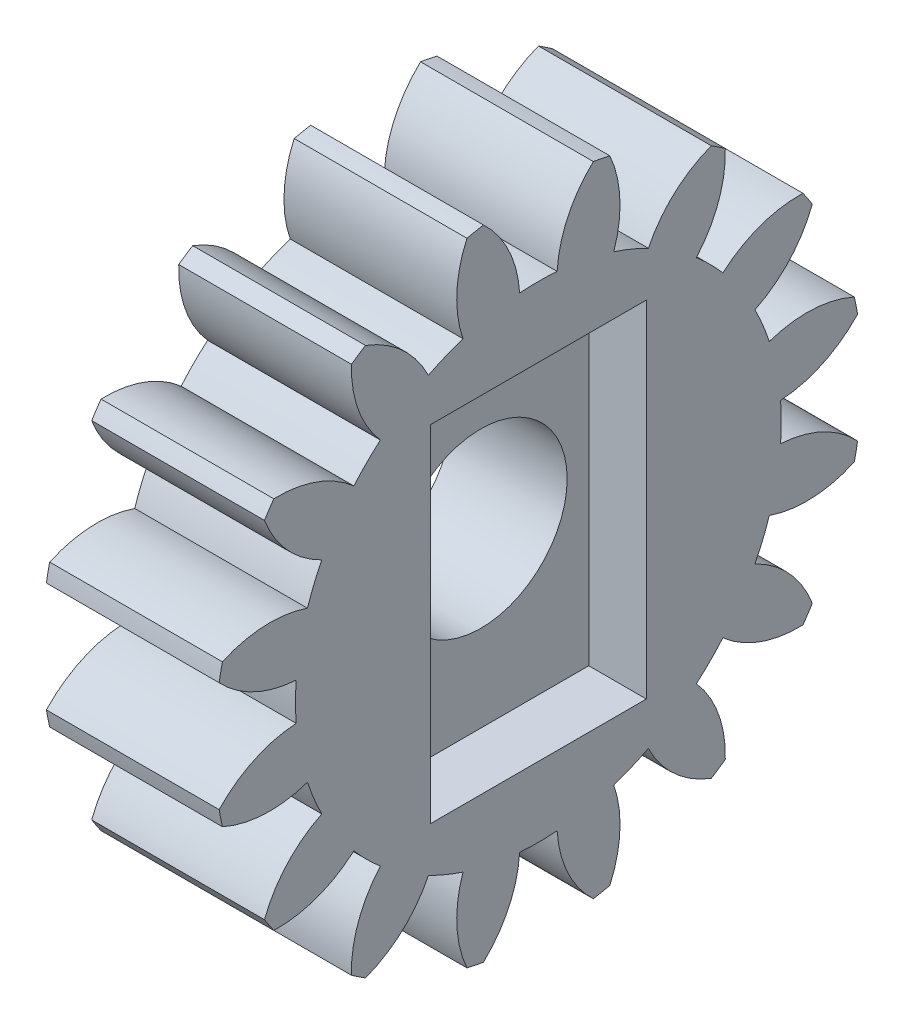
SolidWorks part; units mm, degrees
ref_plane "Plane1" through (0, 0, 0) normal (0, 0, 1) x (1, 0, 0)
ref_plane "Plane2" through (0, 0, 0) normal (0, 1, 0) x (1, 0, 0)
ref_plane "Plane3" through (0, 0, 0) normal (1, 0, 0) x (0, 0, -1)
sketch "HoldingSke" plane through (0, 0, 0) normal (0, 1, 0) x (1, 0, 0)
  line L0 (0, 0) -> (0.769, -0.2205)
  line L1 (-15, 0) -> (100, 0) construction
  line L2 (0, 0) -> (-2.1039, 2.3779)
  line L3 (0, 0) -> (-11.863, 4.5341)
  line L4 (0, 0) -> (8.3015, 2.3804)
  line L5 (0, 0) -> (-46.8476, -17.4728)
  line L6 (0, 0) -> (-4.9738, -3.3558)
  line L7 (-2.1039, 2.3779) -> (8.6586, 51.2059)
  line L8 (-76.2, 54.61) -> (-75.9, 54.61)
  line L9 (-71.009, 38.7566) -> (-53.1078, 45.2721)
  line L10 (-76.2, 71.12) -> (104.1128, 71.12)
  line L11 (0, 0) -> (-6, 0)
  line L12 (-76.2, 101.6) -> (-76.155, 101.6)
  line L13 (24.9733, 27.94) -> (52.9518, 28.4284)
  line L14 (24.9733, 27.94) -> (24.9743, 27.94)
  line L15 (24.9733, 27.94) -> (100.4006, 29.5858)
  line L16 (-63.627, -1.25) -> (-12.827, -1.25)
  circle A0 centre (0, 0) radius 1
  circle A1 centre (0, 0) radius 8.4365
  circle A2 centre (0, 0) radius 37.5
  circle A3 centre (0, 0) radius 1
  dimension "MHD" = 16.873
  dimension "Hub_dia" = 75
  dimension "Bore" = 2
  dimension "MBD" = 2
  dimension "Num_teeth" = 16
  dimension "Pitch" = 0.8
  dimension "Overall_len" = 50
  dimension "Show_teeth" = 16
  dimension "Thickness" = 6
  dimension "OAL" = 50.0001
  dimension "T_dim" = 0.3
  dimension "Ap" = 20
  dimension "H" = 19.05
  dimension "Pitch_radius" = 180.3128
  dimension "Width" = 6
  dimension "Backlash" = 0.045
  dimension "Addendum_fac" = 1
  dimension "Dedendum_fac" = 1.25
  dimension "Clearance_fac" = 0.25
  dimension "Dedendum_add" = 0.001
  dimension "Module" = 1.25
sketch "BasProSke" plane through (0, 0, 0) normal (0, 1, 0) x (1, 0, 0)
  line L0 (-10, 0) -> (60, 0) construction
  line L1 (0, 0) -> (0, 11.25)
  line L2 (0, 0) -> (6, 0)
  line L3 (6, 0) -> (6, 11.25)
  line L4 (6, 11.25) -> (0, 11.25)
  dimension "Thickness" = 6
  dimension "Diameter" = 22.5
revolve "Base-Revolve" add sketch "BasProSke" angle 360 about L0
sketch "TooCutSke" plane through (0, 0, 0) normal (1, 0, 0) x (0, 0, -1)
  line L1 (0, 0) -> (0, 107) construction
  line L2 (0, 0) -> (-1.0589, 9.9438) construction
  line L3 (0, 0) -> (-3.8859, 19.5358) construction
  line L4 (-1.0589, 9.9438) -> (-1.943, 9.7679) construction
  arc A0 (0.6511, 8.4113) -> (-0.6511, 8.4113) centre (0, 0) ccw
  arc A1 (1.9309, 11.1088) -> (-1.9309, 11.1088) centre (0, 0) ccw
  circle A2 centre (0, 0) radius 10 construction
  circle A3 centre (0, 0) radius 9.3969 construction
  arc A4 (-0.6511, 8.4113) -> (-1.9309, 11.1088) centre (-4.6437, 8.1693) ccw
  arc A5 (1.9309, 11.1088) -> (0.6511, 8.4113) centre (4.6437, 8.1693) ccw
  dimension "Root_dia" = 16.873
  dimension "Overcut_dia" = 22.5508
  dimension "Pitch_dia" = 20
  dimension "Base_dia" = 18.7939
  dimension "Flank_rad" = 4
  dimension "Half_ang" = 11.25
  dimension "Half_CT" = 0.9014
extrude "ToothCut" cut sketch "TooCutSke" along normal through all
fillet "Breaks" [suppressed] radius 0.025
fillet "RootFillets" [suppressed] radius 0.3135
pattern_circular "TeethCuts" count 16 every 22.5 about axis through (-10, 0, 0) along (1, 0, 0) of "ToothCut", "RootFillets", "Breaks"
sketch "HubNeaOneSke" plane through (0, 0, 0) normal (-1, 0, 0) x (0, 0, 1)
  circle A0 centre (0, 0) radius 8.4365
  dimension "Diameter" = 16.873
extrude "HubNearOne" [suppressed] add sketch "HubNeaOneSke" along normal blind 44.0001
sketch "HubNeaBotSke" plane through (0, 0, 0) normal (-1, 0, 0) x (0, 0, 1)
  circle A0 centre (0, 0) radius 8.4365
  dimension "Diameter" = 16.873
extrude "HubNearBoth" [suppressed] add sketch "HubNeaBotSke" along normal blind 22
ref_plane "FarPln" through (6, 0, 0) normal (1, 0, 0) x (0, 0, -1)
sketch "HubFarSke" plane through (6, 0, 0) normal (1, 0, 0) x (0, 0, -1)
  circle A0 centre (0, 0) radius 8.4365
  dimension "Diameter" = 16.873
extrude "HubFar" [suppressed] add sketch "HubFarSke" along normal blind 22
sketch "BorSke" plane through (0, 0, 0) normal (1, 0, 0) x (0, 0, -1)
  circle A0 centre (0, 0) radius 3
  dimension "D1" = 6
extrude "Bore" cut sketch "BorSke" along normal mid plane 100.0001
sketch "KeySke" plane through (0, 0, 0) normal (1, 0, 0) x (0, 0, -1)
  line L0 (-0.4, 0) -> (-0.4, 1.3)
  line L1 (-0.4, 1.3) -> (0.4, 1.3)
  line L2 (0.4, 1.3) -> (0.4, 0)
  line L3 (0, 0) -> (0, 34) construction
  line L4 (-0.4, 0) -> (0.4, 0)
  dimension "Offset" = 1.3
  dimension "Width" = 0.8
extrude "Keyway" [suppressed] cut sketch "KeySke" along normal mid plane 100.0001
pattern_circular "Keyway2" [suppressed] count 2 every 90 about axis through (-10, 0, 0) along (1, 0, 0)
sketch "Эскиз1" plane through (6, 0, 0) normal (1, 0, 0) x (0, 0, -1)
  line L0 (0, 7.148) -> (0, -6.7262) construction
  line L1 (-7.5704, 0) -> (7.5314, 0) construction
  line L3 (-3.75, 6) -> (3.75, 6)
  line L4 (-3.75, 6) -> (-3.75, -6)
  line L5 (-3.75, -6) -> (3.75, -6)
  line L6 (3.75, 6) -> (3.75, -6)
  dimension "D1" = 7.5
  dimension "D2" = 12
extrude "Вырез-Вытянуть1" cut sketch "Эскиз1" against normal blind 2
equation "' \"Module@HoldingSke\" = 6.35"
equation "' \"Num_teeth@HoldingSke\" = 12"
equation "' \"Ap@HoldingSke\" =  20"
equation "' \"Ap@HoldingSke\" = 20"
equation "' \"Width@HoldingSke\" = 0.5 * 25.4"
equation "' \"Hub_dia@HoldingSke\"= 1 * 25.4"
equation "' \"Hub_dia@HoldingSke\" = 1 * 25.4"
equation "' \"Overall_len@HoldingSke\" = 1.0 * 25.4"
equation "' \"Bore@HoldingSke\" = 0.75 * 25.4"
equation "' \"T_dim@HoldingSke\" = 0.1 * 25.4"
equation "' \"Width@KeySke\" = 0.25 * 25.4"
equation "' \"Show_teeth@HoldingSke\" = 13"
equation "' \"Backlash@HoldingSke\" = 0.009 * 25.4"
equation "' \"Addendum_fac@HoldingSke\" = 1.0"
equation "' \"Dedendum_fac@HoldingSke\" = 1.25"
equation "' \"Dedendum_add@HoldingSke\" = 0.00005 * 25.4"
equation "' \"Clearance_fac@HoldingSke\" = 0.25"
equation "\"Pitch@HoldingSke\" = 1 / \"Module@HoldingSke\""
equation "\"Overcut_dia@TooCutSke\" = (\"Num_teeth@HoldingSke\" + 2 * \"Addendum_fac@HoldingSke\") / \"Pitch@HoldingSke\" + 0.002 * 25.4"
equation "\"Pitch_dia@TooCutSke\" = \"Num_teeth@HoldingSke\" / \"Pitch@HoldingSke\""
equation "\"Base_dia@TooCutSke\" = \"Num_teeth@HoldingSke\" / \"Pitch@HoldingSke\" * cos((\"Ap@HoldingSke\"  * 3.14159265 / 180))"
equation "\"Root_dia@TooCutSke\" = (\"Num_teeth@HoldingSke\" + 2) / \"Pitch@HoldingSke\" - 2 * (\"Addendum_fac@HoldingSke\" + \"Dedendum_fac@HoldingSke\") / \"Pitch@HoldingSke\" - \"Dedendum_add@HoldingSke\" * 2"
equation "\"Half_ang@TooCutSke\" = 180 / \"Num_teeth@HoldingSke\""
equation "\"Half_CT@TooCutSke\" = \"Num_teeth@HoldingSke\" / \"Pitch@HoldingSke\" * sin((3.14159265 / 2 / \"Num_teeth@HoldingSke\")) / 2 - 7 * \"Backlash@HoldingSke\" / 4"
equation "\"Flank_rad@TooCutSke\" = \"Num_teeth@HoldingSke\" / \"Pitch@HoldingSke\" / 5"
equation "\"Radius@RootFillets\" = \"Clearance_fac@HoldingSke\" / \"Pitch@HoldingSke\" + \"Dedendum_add@HoldingSke\""
equation "\"Break_rad@Breaks\" = 0.02 / \"Pitch@HoldingSke\""
equation "\"Thickness@HoldingSke\" = \"Width@HoldingSke\""
equation "\"OAL@HoldingSke\" = \"Thickness@HoldingSke\""
equation "\"MHD@HoldingSke\" = (\"Num_teeth@HoldingSke\" + 2) / \"Pitch@HoldingSke\" - 2 * (\"Addendum_fac@HoldingSke\" + \"Dedendum_fac@HoldingSke\")  / \"Pitch@HoldingSke\" - \"Dedendum_add@HoldingSke\" * 2"
equation "\"MBD@HoldingSke\" = (\"Num_teeth@HoldingSke\" + 2) / \"Pitch@HoldingSke\" - 2 * (\"Addendum_fac@HoldingSke\" + \"Dedendum_fac@HoldingSke\")  / \"Pitch@HoldingSke\" - \"Dedendum_add@HoldingSke\" * 2 - 0.002 * 25.4"
equation "\"MHD@HoldingSke\" = ((sgn( \"MHD@HoldingSke\" - \"Hub_dia@HoldingSke\" )-1)*( \"MHD@HoldingSke\" - \"Hub_dia@HoldingSke\" ))/-2+ \"Hub_dia@HoldingSke\""
equation "\"MBD@HoldingSke\" = ((sgn( \"MBD@HoldingSke\" - \"Bore@HoldingSke\" )-1)*( \"MBD@HoldingSke\" - \"Bore@HoldingSke\" ))/-2+ \"Bore@HoldingSke\""
equation "\"OAL@HoldingSke\" = ((sgn( \"OAL@HoldingSke\" - \"Overall_len@HoldingSke\" )+1)*( \"OAL@HoldingSke\" - \"Overall_len@HoldingSke\" ))/2 + \"Overall_len@HoldingSke\" + 0.000002 * 25.4"
equation "\"Num_teeth@TeethCuts\" = int( \"Show_teeth@HoldingSke\" ) + 1"
equation "\"Num_teeth@TeethCuts\" = ((sgn( \"Num_teeth@TeethCuts\" - \"Num_teeth@HoldingSke\" )-1)*( \"Num_teeth@TeethCuts\" - \"Num_teeth@HoldingSke\" ))/-2+ \"Num_teeth@HoldingSke\""
equation "\"Num_teeth@TeethCuts\" = ((sgn( \"Num_teeth@TeethCuts\" - 2.0)+1)*( \"Num_teeth@TeethCuts\" - 2.0))/2 +2.0"
equation "\"Angle@TeethCuts\" = 360.0 / \"Num_teeth@HoldingSke\""
equation "\"Diameter@BasProSke\" = (\"Num_teeth@HoldingSke\" + 2 * \"Addendum_fac@HoldingSke\") / \"Pitch@HoldingSke\""
equation "\"Thickness@BasProSke\"  = \"Thickness@HoldingSke\""
equation "' \"Fillet_rad@BasProSke\" =  \"Thickness@HoldingSke\" * 0.05"
equation "' \"Fillet_rad@BasProSke\" = \"Thickness@HoldingSke\" * 0.05"
equation "\"MHD@HoldingSke\" = ((sgn( \"MHD@HoldingSke\" - \"Root_dia@TooCutSke\" )-1)*( \"MHD@HoldingSke\" - \"Root_dia@TooCutSke\" ))/-2+ \"Root_dia@TooCutSke\""
equation "\"Diameter@HubNeaOneSke\" = \"MHD@HoldingSke\""
equation "\"Length@HubNearOne\" = \"OAL@HoldingSke\" - \"Thickness@BasProSke\""
equation "\"Diameter@HubNeaBotSke\" = \"MHD@HoldingSke\""
equation "\"Length@HubNearBoth\" = ( \"OAL@HoldingSke\" - \"Thickness@BasProSke\" ) / 2.0"
equation "\"Thickness@FarPln\" = \"Thickness@BasProSke\""
equation "\"Diameter@HubFarSke\" = \"MHD@HoldingSke\""
equation "\"Length@HubFar\" = ( \"OAL@HoldingSke\" - \"Thickness@BasProSke\" ) / 2.0"
equation "\"D1@Bore\" = \"OAL@HoldingSke\" * 2.0"
equation "\"D1@Keyway\" = \"OAL@HoldingSke\" * 2.0"
equation "\"Offset@KeySke\" = \"T_dim@HoldingSke\" + \"MBD@HoldingSke\" / 2.0"
